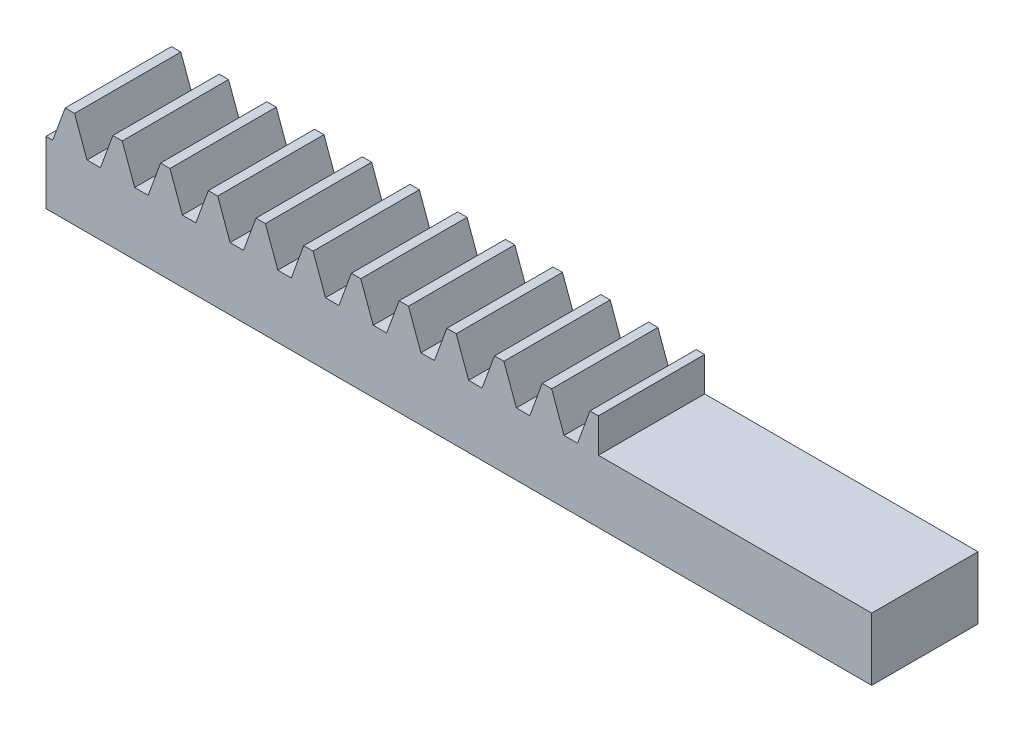
SolidWorks part; units mm, degrees
extrude "Blank" add sketch "BlankSke" against normal blind 2.8
sketch "BlankSke" plane through (0, 0, 0) normal (0, 0, 1) x (1, 0, 0)
  line L1 (0, 0) -> (21.75, 0)
  line L2 (0, 0) -> (0, 2.55)
  line L3 (0, 2.55) -> (21.75, 2.55)
  line L4 (21.75, 0) -> (21.75, 2.55)
  dimension "Length" = 21.75
  dimension "Blank_height" = 2.55
ref_plane "Plane1" through (0, 0, 0) normal (0, 0, 1) x (1, 0, 0)
ref_plane "Plane2" through (0, 0, 0) normal (0, 1, 0) x (1, 0, 0)
ref_plane "Plane3" through (0, 0, 0) normal (1, 0, 0) x (0, 0, -1)
other "Configuration Table"
sketch "HoldingSke" plane through (0, 0, 0) normal (0, 1, 0) x (1, 0, 0)
  line L0 (0, 0) -> (0.3479, 2.4757)
  line L1 (-15, 0) -> (100, 0) construction
  line L2 (0, 0) -> (-2.1039, 2.3779)
  line L3 (0, 0) -> (-11.863, 4.5341)
  line L4 (0, 0) -> (8.1655, 2.8116)
  line L5 (0, 0) -> (-23.7986, -8.8762)
  line L6 (0, 0) -> (-10.5278, -7.1032)
  line L9 (-71.009, 38.7566) -> (-50.5707, 46.1955)
  line L10 (-76.2, 2.7779) -> (-74.05, 2.7779)
  line L11 (0, 0) -> (-2.8, 0)
  line L12 (-76.2, 101.6) -> (-76.185, 101.6)
  line L13 (24.9733, 27.94) -> (52.9518, 28.4284)
  line L14 (24.9733, 27.94) -> (24.9743, 27.94)
  line L15 (24.9733, 27.94) -> (100.4006, 29.5858)
  circle A0 centre (0, 0) radius 19.05
  circle A1 centre (0, 0) radius 1.075
  circle A2 centre (0, 0) radius 12.7
  dimension "MPH" = 2.15
  dimension "Diameter" = 38.1
  dimension "Num_teeth" = 19
  dimension "Pitch" = 2.5
  dimension "Show_teeth" = 998
  dimension "Thickness" = 12.7
  dimension "Ap" = 20
  dimension "Pitch_height" = 2.15
  dimension "Width" = 2.8
  dimension "Backlash" = 0.015
  dimension "Addendum_fac" = 1
  dimension "Dedendum_fac" = 1.25
  dimension "Clearance_fac" = 0.25
  dimension "Dedendum_add" = 0.001
  dimension "Length" = 21.75
  dimension "Module" = 0.4
sketch "TooCutSkeIll" plane through (0, 0, 0) normal (0, 0, 1) x (1, 0, 0)
  line L0 (-0.5009, 2.5395) -> (-0.2014, 1.7165)
  line L1 (-0.1065, 1.65) -> (0.1065, 1.65)
  line L2 (0.2014, 1.7165) -> (0.5009, 2.5395)
  line L3 (21.75, 2.55) -> (0, 2.55) construction
  line L4 (0, 0) -> (0, 64.897) construction
  line L5 (-13.208, 2.15) -> (12.954, 2.15) construction
  line L6 (0, 0) -> (21.75, 0) construction
  line L7 (0.3592, 2.15) -> (0.3592, 48.7463) construction
  line L8 (-0.3592, 2.15) -> (-0.3592, 48.7463) construction
  line L9 (0.516, 2.55) -> (0.516, 2.5754)
  line L10 (-0.516, 2.55) -> (-0.516, 2.5754)
  line L11 (-0.516, 2.5754) -> (0.516, 2.5754)
  arc A0 (0.1065, 1.65) -> (0.2014, 1.7165) centre (0.1065, 1.751) ccw
  arc A1 (-0.2014, 1.7165) -> (-0.1065, 1.65) centre (-0.1065, 1.751) ccw
  arc A2 (0.516, 2.55) -> (0.5009, 2.5395) centre (0.516, 2.534) ccw
  arc A3 (-0.5009, 2.5395) -> (-0.516, 2.55) centre (-0.516, 2.534) ccw
  dimension "Pitch_height" = 2.15
  dimension "Addendum_plus" = 0.4254
  dimension "Pressure_angle" = 20
  dimension "Gap_width" = 0.7183
  dimension "Dedendum" = 0.5
extrude "ToothCutIll" [suppressed] cut sketch "TooCutSkeIll" against normal through all
sketch "TooCutSkeSim" plane through (0, 0, 0) normal (0, 0, 1) x (1, 0, 0)
  line L0 (0.1772, 1.65) -> (-0.1772, 1.65)
  line L1 (0.514, 2.5754) -> (0.1772, 1.65)
  line L2 (0, 17.4625) -> (0, 53.467) construction
  line L3 (0.514, 2.5754) -> (-0.514, 2.5754)
  line L6 (-0.514, 2.5754) -> (-0.1772, 1.65)
  line L9 (-0.3592, 2.15) -> (0.3592, 2.15) construction
  line L10 (0, 0) -> (21.75, 0) construction
  line L11 (0.3592, 2.15) -> (0.3592, 53.467) construction
  line L12 (-0.3592, 2.15) -> (-0.3592, 53.467) construction
  dimension "Pitch_height" = 2.15
  dimension "Addendum_plus" = 0.4254
  dimension "Pressure_angle" = 20
  dimension "Gap_width" = 0.7183
  dimension "Dedendum" = 0.5
extrude "ToothCutSim" cut sketch "TooCutSkeSim" against normal through all
pattern_linear "TeethCuts" count 18 spacing 1.2566 along (1, 0, 0) of "ToothCutIll", "ToothCutSim"
sketch "Sketch1" plane through (0, 0, 0) normal (0, 0, 1) x (1, 0, 0)
  line L0 (21.75, 1.65) -> (14.55, 1.65)
  line L1 (21.75, 0) -> (21.75, 2.227) construction
  line L2 (14.55, 1.65) -> (14.55, 2.55)
  line L3 (14.55, 2.55) -> (21.75, 2.55)
  line L4 (21.75, 2.55) -> (21.75, 1.65)
  dimension "D1" = 7.2
extrude "Cut-Extrude1" cut sketch "Sketch1" against normal through all
equation "' \"Module@HoldingSke\" = 6.35"
equation "' \"Num_teeth@HoldingSke\" = 12"
equation "' \"Ap@HoldingSke\" =  20"
equation "' \"Ap@HoldingSke\" = 20"
equation "' \"Width@HoldingSke\" = 0.25 * 25.4"
equation "' \"Show_teeth@HoldingSke\" = 500"
equation "' \"Backlash@HoldingSke\" = 0.009 * 25.4"
equation "' \"Addendum_fac@HoldingSke\" = 1.0"
equation "' \"Dedendum_fac@HoldingSke\" = 1.25"
equation "' \"Dedendum_add@HoldingSke\" = 0.00005 * 25.4"
equation "' \"Clearance_fac@HoldingSke\" = 0.25"
equation "' \"Pitch_height@HoldingSke\" = 1 * 25.4"
equation "' \"Length@HoldingSke\" = 4.71 * 25.4"
equation "\"Pitch@HoldingSke\" = 1 / \"Module@HoldingSke\""
equation "\"MPH@HoldingSke\" = \"Dedendum_fac@HoldingSke\" / \"Pitch@HoldingSke\" + 2 * \"Dedendum_add@HoldingSke\" + 0.002 * 25.4"
equation "\"MPH@HoldingSke\" = ((sgn( \"MPH@HoldingSke\" - \"Pitch_height@HoldingSke\")+1)*( \"MPH@HoldingSke\" - \"Pitch_height@HoldingSke\"))/2 + \"Pitch_height@HoldingSke\""
equation "\"Blank_height@BlankSke\" = \"Pitch_height@HoldingSke\" + \"Addendum_fac@HoldingSke\"  / \"Pitch@HoldingSke\" "
equation "\"Length@BlankSke\" =  \"Length@HoldingSke\""
equation "\"Face_width@Blank\" = \"Width@HoldingSke\""
equation "\"Pressure_angle@TooCutSkeIll\" = \"Ap@HoldingSke\""
equation "\"Addendum_plus@TooCutSkeIll\" =  \"Addendum_fac@HoldingSke\"  / \"Pitch@HoldingSke\" + 0.001 *25.4"
equation "\"Dedendum@TooCutSkeIll\" = \"Dedendum_fac@HoldingSke\"  / \"Pitch@HoldingSke\""
equation "\"Pitch_height@TooCutSkeIll\" =  \"MPH@HoldingSke\""
equation "\"Gap_width@TooCutSkeIll\" = 3.14159265 / 2 / \"Pitch@HoldingSke\" + 6 * \"Backlash@HoldingSke\""
equation "\"Pressure_angle@TooCutSkeSim\" = \"Ap@HoldingSke\""
equation "\"Addendum_plus@TooCutSkeSim\" =  \"Addendum_fac@HoldingSke\"  / \"Pitch@HoldingSke\" + 0.001 * 25.4"
equation "\"Dedendum@TooCutSkeSim\" = \"Dedendum_fac@HoldingSke\"  / \"Pitch@HoldingSke\""
equation "\"Pitch_height@TooCutSkeSim\" =  \"MPH@HoldingSke\""
equation "\"Gap_width@TooCutSkeSim\" = 3.14159265 / 2 / \"Pitch@HoldingSke\" + 6 * \"Backlash@HoldingSke\""
equation "\"Root_fillet@TooCutSkeIll\" = \"Clearance_fac@HoldingSke\" / \"Pitch@HoldingSke\" + \"Dedendum_add@HoldingSke\""
equation "\"Break_rad@TooCutSkeIll\" = 0.02 / \"Pitch@HoldingSke\" * 2"
equation "\"Linear_pitch@TeethCuts\" = 3.14159265 / \"Pitch@HoldingSke\""
equation "\"Num_teeth@HoldingSke\" = int( ( \"Length@HoldingSke\" + 0 ) / (3.14159265 / \"Pitch@HoldingSke\")) + 0.9999  + 1"
equation " \"Num_teeth@TeethCuts\" = int( \"Show_teeth@HoldingSke\" ) + 1"
equation " \"Num_teeth@TeethCuts\" = ((sgn( \"Num_teeth@TeethCuts\" - \"Num_teeth@HoldingSke\" )-1)*( \"Num_teeth@TeethCuts\" - \"Num_teeth@HoldingSke\" ))/-2+ \"Num_teeth@HoldingSke\""
equation " \"Num_teeth@TeethCuts\" = ((sgn( \"Num_teeth@TeethCuts\" - 2.0)+1)*( \"Num_teeth@TeethCuts\" - 2.0))/2 +2.0"
